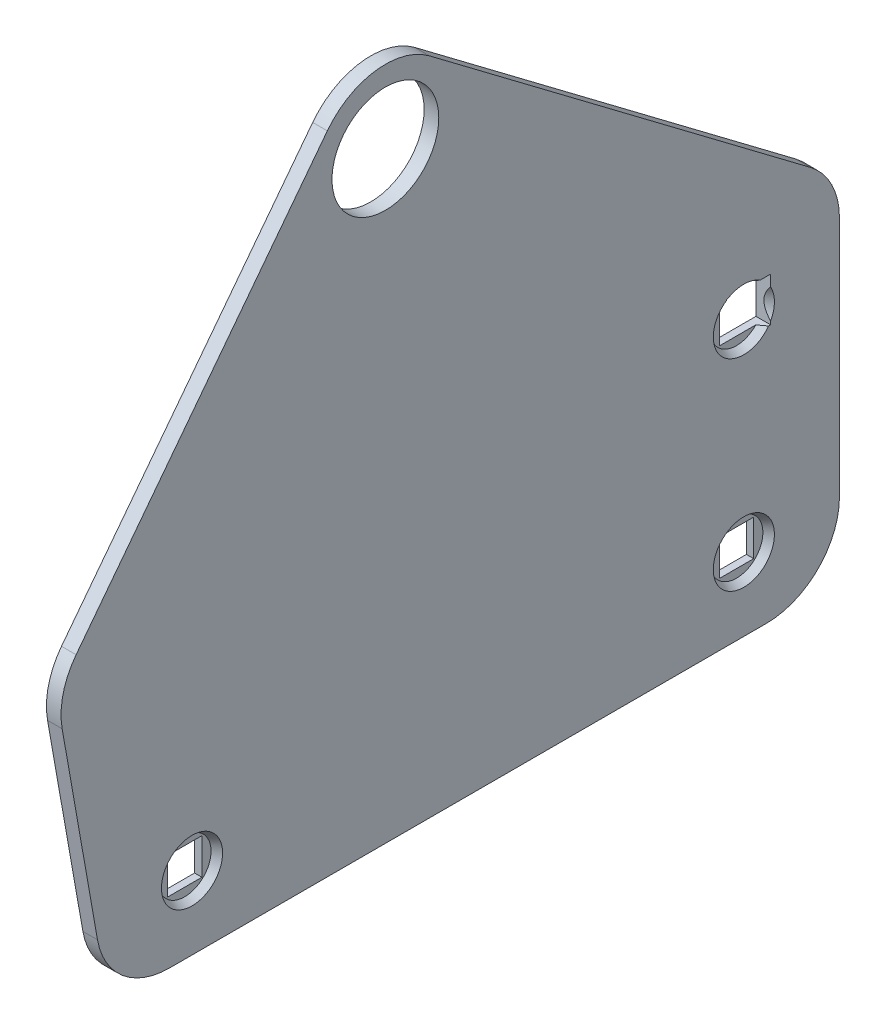
SolidWorks part; units mm, degrees
ref_plane "Front Plane" through (0, 0, 0) normal (0, 0, 1) x (1, 0, 0)
ref_plane "Top Plane" through (0, 0, 0) normal (0, 1, 0) x (1, 0, 0)
ref_plane "Right Plane" through (0, 0, 0) normal (1, 0, 0) x (0, 0, -1)
sketch "Sketch1" plane through (0, 0, 0) normal (1, 0, 0) x (0, 0, -1)
  line L0 (-20.4023, 0) -> (20.4023, 0)
  line L1 (-25.3263, 4.1318) -> (-27.7428, 17.8364)
  line L3 (-28.1243, 20) -> (-28.1243, 34.7886) construction
  line L4 (-28.1243, 20) -> (-6.1364, 20) construction
  line L5 (25.4023, 5) -> (25.4023, 21.5071)
  line L7 (25.4023, 24) -> (46.436, 24) construction
  line L9 (23.4113, 25.5003) -> (-2.6352, 45.1277)
  line L11 (-24.5977, 0) -> (-19.2077, 0) construction
  line L12 (-18.865, 2.91) -> (-18.865, 0) construction
  line L13 (0, 0) -> (0, 24.9763) construction
  line L23 (17.6918, 17.54) -> (20.6918, 17.54)
  line L24 (17.6918, 17.54) -> (17.6918, 20.54)
  line L25 (17.6918, 20.54) -> (20.6918, 20.54)
  line L26 (20.6918, 17.54) -> (20.6918, 20.54)
  line L29 (-9.6142, 44.1743) -> (-26.7886, 21.7444)
  line L30 (20.04, 3.77) -> (17.69, 3.77)
  line L31 (-20.04, 6.23) -> (-17.69, 6.23)
  line L32 (-20.04, 6.23) -> (-20.04, 3.77)
  line L33 (-20.04, 3.77) -> (-17.69, 3.77)
  line L34 (-17.69, 3.77) -> (-17.69, 6.23)
  line L35 (17.69, 3.77) -> (17.69, 6.23)
  line L36 (20.04, 6.23) -> (17.69, 6.23)
  line L37 (20.04, 6.23) -> (20.04, 3.77)
  arc A5 (20.4023, 0) -> (25.4023, 5) centre (20.4023, 5) ccw
  arc A6 (-20.4023, 0) -> (-25.3263, 4.1318) centre (-20.4023, 5) cw
  arc A7 (25.4023, 21.5071) -> (23.4113, 25.5003) centre (20.4023, 21.5071) ccw
  arc A8 (-27.7428, 17.8364) -> (-26.7886, 21.7444) centre (-22.8187, 18.7046) cw
  arc A9 (-2.6352, 45.1277) -> (-9.6142, 44.1743) centre (-5.6443, 41.1346) ccw
  circle A10 centre (-5.6443, 41.1346) radius 3.65
  point P2 (0, 0)
  point P35 (25.4023, 0)
  dimension "D9" = 3
  dimension "D12" = 2.6352
  dimension "D6" = 7.3
  dimension "D13" = 5
  dimension "D1" = 50
  dimension "D2" = 100
  dimension "D3" = 20
  dimension "D4" = 143
  dimension "D5" = 24
  dimension "D7" = 3
  dimension "D14" = 2.46
  dimension "D15" = 2.35
extrude "Boss-Extrude1" add sketch "Sketch1" along normal blind 1
sketch "Sketch3" plane through (1, 0, 0) normal (1, 0, 0) x (0, 0, -1)
  circle A0 centre (-18.865, 5) radius 2.09
  circle A1 centre (18.865, 5) radius 2.09
  circle A2 centre (18.865, 18.77) radius 2.09
extrude "Cut-Extrude1" cut sketch "Sketch3" against normal blind 0.5 draft 30
